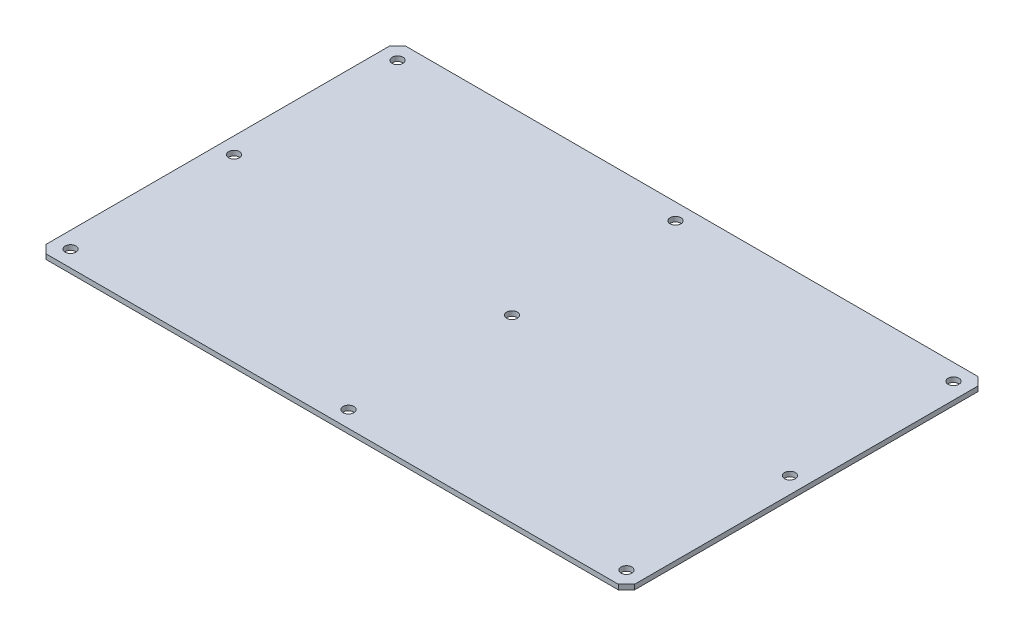
SolidWorks part; units mm, degrees
material "PC High Viscosity"
ref_plane "Plan de face" through (0, 0, 0) normal (0, 0, 1) x (1, 0, 0)
ref_plane "Plan de dessus" through (0, 0, 0) normal (0, 1, 0) x (1, 0, 0)
ref_plane "Plan de droite" through (0, 0, 0) normal (1, 0, 0) x (0, 0, -1)
sketch "Esquisse1" plane through (0, 0, 0) normal (0, 1, 0) x (1, 0, 0)
  line L0 (-180, 0) -> (180, 0) construction
  line L1 (180, 110) -> (-180, 110)
  line L2 (180, 110) -> (180, -110)
  line L3 (180, -110) -> (-180, -110)
  line L4 (-180, 110) -> (-180, -110)
  line L6 (0, 110) -> (0, -110) construction
  line L7 (170, -100) -> (-170, -100) construction
  line L8 (170, -100) -> (170, 100) construction
  line L9 (170, 100) -> (-170, 100) construction
  line L10 (-170, -100) -> (-170, 100) construction
  line L11 (170, -100) -> (-170, 100) construction
  line L12 (170, 100) -> (-170, -100) construction
  point P7 (0, 0)
  dimension "D1" = 360
  dimension "D2" = 220
  dimension "D3" = 340
  dimension "D4" = 200
  dimension "D5" = 10
  dimension "D6" = 10
extrude "Boss.-Extru.1" add sketch "Esquisse1" along normal blind 3
hole_wizard "M6 Clearance Hole1" positions "Sketch1" profile "Sketch2" hole size "M6" standard "ISO" end condition through all
sketch "Sketch1" plane through (0, 0, 0) normal (0, -1, 0) x (-1, 0, 0)
  line L0 (-170, 100) -> (0, 100) construction
  line L1 (-170, 100) -> (-170, 0) construction
  point P0 (-170, 100)
  point P6 (0, 100)
  point P7 (170, 100)
  point P8 (0, 0)
  point P9 (170, 0)
  point P10 (0, -100)
  point P11 (170, -100)
  point P12 (-170, 0)
  point P13 (-170, -100)
  dimension "D3" = 170
  dimension "D4" = 100
  dimension "D1" = 3
  dimension "D2" = 3
sketch "Sketch2" plane through (170, 0, -100) normal (1, 0, 0) x (0, 0, -1)
  line L0 (0, 0) -> (0, 3)
  line L1 (0, 3) -> (3.3, 3)
  line L2 (3.3, 3) -> (3.3, 0)
  line L5 (3.3, 0) -> (0, 0)
  line L11 (0, -6.35) -> (0, 107.95) construction
  dimension "Diámetro de taladro hasta el siguiente" = 6.6
  dimension "Profundidad de taladro hasta el siguiente" = 3
chamfer "Chamfer1" distance 5 angle 45 4 edges at (-180, 1.5, 110) (180, 1.5, 110) (180, 1.5, -110) (-180, 1.5, -110)
